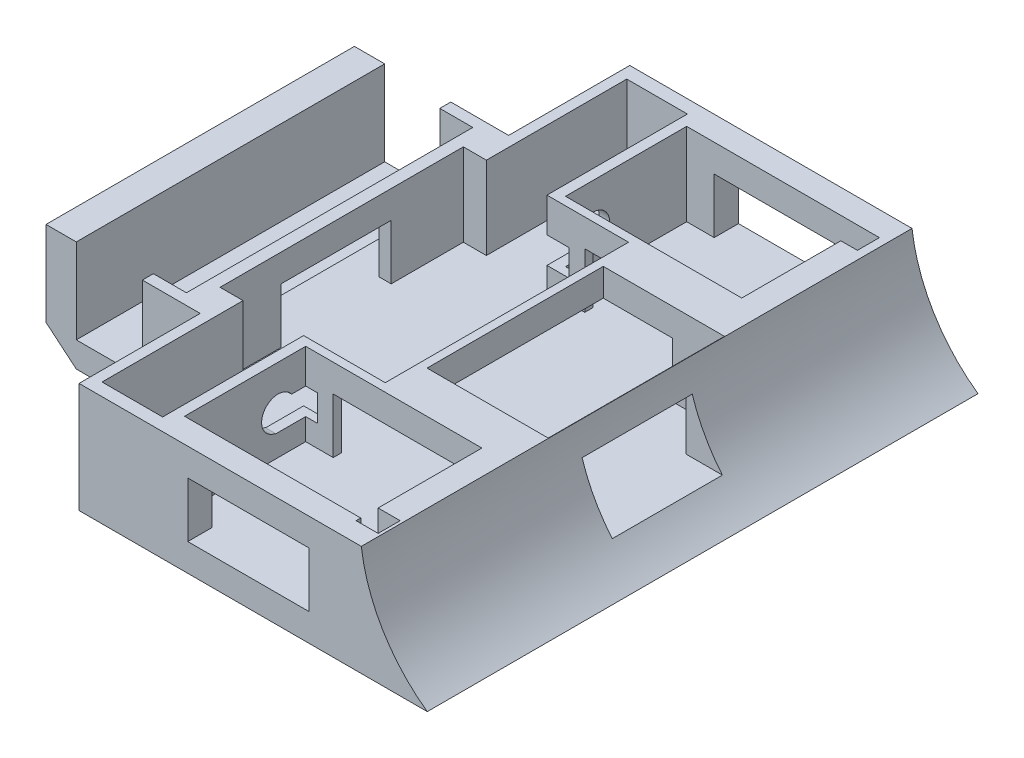
SolidWorks part; units mm, degrees
ref_plane "Front Plane" through (0, 0, 0) normal (0, 0, 1) x (1, 0, 0)
ref_plane "Top Plane" through (0, 0, 0) normal (0, 1, 0) x (1, 0, 0)
ref_plane "Right Plane" through (0, 0, 0) normal (1, 0, 0) x (0, 0, -1)
sketch "Sketch1" plane through (0, 0, 0) normal (0, 1, 0) x (1, 0, 0)
  line L1 (-50, -50) -> (50, -50)
  line L2 (-50, -50) -> (-50, 50)
  line L3 (-50, 50) -> (50, 50)
  line L4 (50, -50) -> (50, 50)
  line L5 (-50, -50) -> (50, 50) construction
  line L6 (-50, 50) -> (50, -50) construction
  point P0 (0, 0)
  dimension "D1" = 100
  dimension "D2" = 100
extrude "Boss-Extrude2" add sketch "Sketch1" along normal blind 40
sketch "Sketch3" plane through (50, 0, 0) normal (1, 0, 0) x (0, 0, -1)
  line L0 (-50, 40) -> (50, 40) construction
  line L1 (-11.0102, 5) -> (8.9898, 5)
  line L2 (-11.0102, 5) -> (-11.0102, 15)
  line L3 (-11.0102, 15) -> (8.9898, 15)
  line L4 (8.9898, 5) -> (8.9898, 15)
  line L5 (-11.0102, 5) -> (8.9898, 15) construction
  line L6 (-11.0102, 15) -> (8.9898, 5) construction
  line L8 (-50, 40) -> (-50, 0) construction
  point P0 (-1.0102, 10)
  point P7 (-50, 20)
  dimension "D1" = 20
  dimension "D2" = 10
  dimension "D3" = 30
  dimension "D4" = 50
extrude "Cut-Extrude3" cut sketch "Sketch3" against normal blind 100
sketch "Sketch4" plane through (0, 0, 50) normal (0, 0, 1) x (1, 0, 0)
  circle A0 centre (63.1914, 23.7473) radius 29.1799
extrude "Cut-Extrude5" cut sketch "Sketch4" against normal blind 100
sketch "Sketch5" plane through (0, 0, 50) normal (0, 0, 1) x (1, 0, 0)
  line L1 (-21.0432, 20) -> (38.9568, 20)
  line L2 (-21.0432, 20) -> (-21.0432, 40)
  line L3 (-21.0432, 40) -> (38.9568, 40)
  line L4 (38.9568, 20) -> (38.9568, 40)
  line L5 (-21.0432, 20) -> (38.9568, 40) construction
  line L6 (-21.0432, 40) -> (38.9568, 20) construction
  point P0 (8.9568, 30)
  dimension "D1" = 20
  dimension "D2" = 60
extrude "Cut-Extrude6" cut sketch "Sketch5" against normal blind 100
sketch "Sketch6" plane through (0, 20, 0) normal (0, 1, 0) x (1, 0, 0)
  line L1 (12.1904, -16) -> (34.1904, -16)
  line L2 (12.1904, -16) -> (12.1904, 16)
  line L3 (12.1904, 16) -> (34.1904, 16)
  line L4 (34.1904, -16) -> (34.1904, 16)
  line L5 (12.1904, -16) -> (34.1904, 16) construction
  line L6 (12.1904, 16) -> (34.1904, -16) construction
  point P0 (23.1904, 0)
  dimension "D1" = 32
  dimension "D2" = 22
extrude "Cut-Extrude7" cut sketch "Sketch6" against normal blind 15
sketch "Sketch7" plane through (0, 0, 50) normal (0, 0, 1) x (1, 0, 0)
  line L0 (-50, 0) -> (46.2347, 0) construction
  line L1 (2.7431, 15) -> (24.7431, 15)
  line L2 (2.7431, 15) -> (2.7431, 5)
  line L3 (2.7431, 5) -> (24.7431, 5)
  line L4 (24.7431, 15) -> (24.7431, 5)
  line L5 (2.7431, 15) -> (24.7431, 5) construction
  line L6 (2.7431, 5) -> (24.7431, 15) construction
  point P0 (13.7431, 10)
  dimension "D1" = 10
  dimension "D2" = 22
  dimension "D3" = 5
extrude "Cut-Extrude9" cut sketch "Sketch7" against normal blind 100
sketch "Sketch9" plane through (0, 20, 0) normal (0, 1, 0) x (1, 0, 0)
  line L1 (-2.2569, -45.5889) -> (29.7431, -45.5889)
  line L2 (-2.2569, -45.5889) -> (-2.2569, -23.5889)
  line L3 (-2.2569, -23.5889) -> (29.7431, -23.5889)
  line L4 (29.7431, -45.5889) -> (29.7431, -23.5889)
  line L5 (-2.2569, -45.5889) -> (29.7431, -23.5889) construction
  line L6 (-2.2569, -23.5889) -> (29.7431, -45.5889) construction
  point P0 (13.7431, -34.5889)
  dimension "D1" = 32
  dimension "D2" = 22
  dimension "D3" = 5
  dimension "D4" = 5
extrude "Cut-Extrude10" cut sketch "Sketch9" against normal blind 15
sketch "Sketch10" plane through (0, 20, 0) normal (0, 1, 0) x (1, 0, 0)
  line L0 (-2.2569, -45.5889) -> (29.7431, -45.5889) construction
  line L1 (29.7431, 45.59) -> (-2.2569, 45.59)
  line L2 (29.7431, 45.59) -> (29.7431, 23.59)
  line L3 (29.7431, 23.59) -> (-2.2569, 23.59)
  line L4 (-2.2569, 45.59) -> (-2.2569, 23.59)
  line L5 (29.7431, 45.59) -> (-2.2569, 23.59) construction
  line L6 (29.7431, 23.59) -> (-2.2569, 45.59) construction
  line L8 (-21.0432, 50) -> (34.2532, 50) construction
  point P0 (13.7431, 34.59)
  dimension "D1" = 32
  dimension "D2" = 22
  dimension "D3" = 4.41
  dimension "D4" = 5
extrude "Cut-Extrude11" cut sketch "Sketch10" against normal blind 15
sketch "Sketch11" plane through (0, 0, 50) normal (0, 0, 1) x (1, 0, 0)
  line L1 (-50, 0) -> (-17, 0)
  line L2 (-50, 0) -> (-50, 33)
  line L3 (-50, 33) -> (-17, 33)
  line L4 (-17, 0) -> (-17, 33)
  dimension "D1" = 33
  dimension "D2" = 33
extrude "Cut-Extrude13" cut sketch "Sketch11" against normal blind 22
sketch "Sketch12" plane through (0, 0, -50) normal (0, 0, -1) x (-1, 0, 0)
  line L1 (50, 0) -> (17, 0)
  line L2 (50, 0) -> (50, 33)
  line L3 (50, 33) -> (17, 33)
  line L4 (17, 0) -> (17, 33)
  dimension "D1" = 33
  dimension "D2" = 33
extrude "Cut-Extrude14" cut sketch "Sketch12" against normal blind 22
sketch "Sketch13" plane through (0, 0, -50) normal (0, 0, -1) x (-1, 0, 0)
  line L1 (21.0432, 40) -> (51.0432, 40)
  line L2 (21.0432, 40) -> (21.0432, 20)
  line L3 (21.0432, 20) -> (51.0432, 20)
  line L4 (51.0432, 40) -> (51.0432, 20)
  dimension "D1" = 30
  dimension "D2" = 20
extrude "Cut-Extrude15" cut sketch "Sketch13" against normal blind 100
sketch "Sketch14" plane through (0, 0, 28) normal (0, 0, 1) x (1, 0, 0)
  line L0 (-50, 20) -> (-50, 0) construction
  line L1 (-39.5, 4.5951) -> (-27.5, 4.5951)
  line L2 (-39.5, 4.5951) -> (-39.5, 20.5951)
  line L3 (-39.5, 20.5951) -> (-27.5, 20.5951)
  line L4 (-27.5, 4.5951) -> (-27.5, 20.5951)
  line L5 (-39.5, 4.5951) -> (-27.5, 20.5951) construction
  line L6 (-39.5, 20.5951) -> (-27.5, 4.5951) construction
  point P0 (-33.5, 12.5951)
  dimension "D1" = 12
  dimension "D2" = 16
  dimension "D3" = 10.5
extrude "Cut-Extrude17" cut sketch "Sketch14" against normal blind 80
sketch "Sketch15" plane through (0, 20, 0) normal (0, 1, 0) x (1, 0, 0)
  line L0 (-39.5, -28) -> (-39.5, 28) construction
  line L1 (-45.5, -26) -> (-21.5, -26)
  line L2 (-45.5, -26) -> (-45.5, 26)
  line L3 (-45.5, 26) -> (-21.5, 26)
  line L4 (-21.5, -26) -> (-21.5, 26)
  line L5 (-50, 28) -> (-39.5, 28) construction
  point P7 (-44.75, 28)
  dimension "D1" = 24
  dimension "D2" = 52
  dimension "D3" = 6
  dimension "D4" = 6
  dimension "D5" = 2
extrude "Cut-Extrude18" cut sketch "Sketch15" against normal blind 15
sketch "Sketch16" plane through (0, 20, 0) normal (0, 1, 0) x (1, 0, 0)
  line L0 (29.7431, -23.5889) -> (-2.2569, -23.5889) construction
  line L1 (-19.3096, 22.0911) -> (10.6904, 22.0911)
  line L2 (-19.3096, 22.0911) -> (-19.3096, -22.0889)
  line L3 (-19.3096, -22.0889) -> (10.6904, -22.0889)
  line L4 (10.6904, 22.0911) -> (10.6904, -22.0889)
  line L5 (-19.3096, 22.0911) -> (10.6904, -22.0889) construction
  line L6 (-19.3096, -22.0889) -> (10.6904, 22.0911) construction
  point P0 (-4.3096, 0.0011)
  dimension "D1" = 44.18
  dimension "D2" = 30
  dimension "D3" = 1.5
  dimension "D4" = 1.5
  dimension "D5" = 1.4989
extrude "Cut-Extrude19" cut sketch "Sketch16" against normal blind 15
sketch "Sketch17" plane through (0, 20, 0) normal (0, 1, 0) x (1, 0, 0)
  line L1 (-4.1269, 47.59) -> (-15.1269, 47.59)
  line L2 (-4.1269, 47.59) -> (-4.1269, 21.59)
  line L3 (-4.1269, 21.59) -> (-15.1269, 21.59)
  line L4 (-15.1269, 47.59) -> (-15.1269, 21.59)
  line L5 (-4.1269, 47.59) -> (-15.1269, 21.59) construction
  line L6 (-4.1269, 21.59) -> (-15.1269, 47.59) construction
  point P0 (-9.6269, 34.59)
  dimension "D1" = 26
  dimension "D2" = 11
  dimension "D3" = 2
  dimension "D4" = 2
  dimension "D5" = 1.87
  dimension "D6" = 1.8731
extrude "Cut-Extrude20" cut sketch "Sketch17" against normal blind 15
sketch "Sketch18" plane through (0, 20, 0) normal (0, 1, 0) x (1, 0, 0)
  line L1 (-15.13, -21.6911) -> (-4.13, -21.6911)
  line L2 (-15.13, -21.6911) -> (-15.13, -47.6911)
  line L3 (-15.13, -47.6911) -> (-4.13, -47.6911)
  line L4 (-4.13, -21.6911) -> (-4.13, -47.6911)
  line L5 (-15.13, -21.6911) -> (-4.13, -47.6911) construction
  line L6 (-15.13, -47.6911) -> (-4.13, -21.6911) construction
  point P0 (-9.63, -34.6911)
  dimension "D1" = 26
  dimension "D2" = 11
  dimension "D3" = 1.87
  dimension "D4" = 1.8731
extrude "Cut-Extrude22" cut sketch "Sketch18" against normal blind 15
sketch "Sketch19" plane through (0, 0, 0) normal (0, -1, 0) x (-1, 0, 0)
  line L0 (-46.2347, -50) -> (-46.2347, 50) construction
  line L1 (-43.2347, -45) -> (-32.2347, -45)
  line L2 (-43.2347, -45) -> (-43.2347, -28)
  line L3 (-43.2347, -28) -> (-32.2347, -28)
  line L4 (-32.2347, -45) -> (-32.2347, -28)
  line L5 (-43.2347, -45) -> (-32.2347, -28) construction
  line L6 (-43.2347, -28) -> (-32.2347, -45) construction
  line L7 (17, -50) -> (-46.2347, -50) construction
  point P0 (-37.7347, -36.5)
  dimension "D1" = 17
  dimension "D2" = 11
  dimension "D3" = 3
  dimension "D4" = 5
extrude "Cut-Extrude26" cut sketch "Sketch19" against normal blind 2.2
sketch "Sketch20" plane through (0, 0, 0) normal (0, -1, 0) x (-1, 0, 0)
  circle A0 centre (-32.2347, -45) radius 2.5
extrude "Cut-Extrude32" cut sketch "Sketch20" against normal blind 17
sketch "Sketch21" plane through (29.7431, 0, 0) normal (-1, 0, 0) x (0, 0, 1)
  line L0 (45.5889, 20) -> (23.5889, 20) construction
  line L1 (46.4334, 20) -> (42.4334, 20)
  line L2 (46.4334, 20) -> (46.4334, 8)
  line L3 (46.4334, 8) -> (42.4334, 8)
  line L4 (42.4334, 20) -> (42.4334, 8)
  dimension "D1" = 4
  dimension "D2" = 12
extrude "Cut-Extrude33" cut sketch "Sketch21" against normal blind 4
sketch "Sketch23" plane through (0, 0, 0) normal (0, -1, 0) x (-1, 0, 0)
  line L0 (-46.2347, 50) -> (17, 50) construction
  line L1 (-32.2347, 45) -> (-43.2347, 45)
  line L2 (-32.2347, 45) -> (-32.2347, 28)
  line L3 (-32.2347, 28) -> (-43.2347, 28)
  line L4 (-43.2347, 45) -> (-43.2347, 28)
  line L5 (-46.2347, -50) -> (-46.2347, 50) construction
  dimension "D1" = 17
  dimension "D2" = 11
  dimension "D3" = 5
  dimension "D4" = 3
extrude "Cut-Extrude34" cut sketch "Sketch23" against normal blind 2.2
sketch "Sketch24" plane through (0, 0, 0) normal (0, -1, 0) x (1, 0, 0)
  circle A0 centre (32.2347, -45) radius 2.5
extrude "Cut-Extrude35" cut sketch "Sketch24" against normal blind 17
sketch "Sketch25" plane through (29.7431, 0, 0) normal (-1, 0, 0) x (0, 0, 1)
  line L1 (-45.59, 20) -> (-41.59, 20)
  line L2 (-45.59, 20) -> (-45.59, 8)
  line L3 (-45.59, 8) -> (-41.59, 8)
  line L4 (-41.59, 20) -> (-41.59, 8)
  dimension "D1" = 4
  dimension "D2" = 12
extrude "Cut-Extrude36" cut sketch "Sketch25" against normal blind 3
sketch "Sketch26" plane through (-2.2569, 0, 0) normal (1, 0, 0) x (0, 0, -1)
  line L0 (-23.5889, 20) -> (-45.5889, 20) construction
  line L1 (-23.5889, 5) -> (-23.5889, 20) construction
  circle A0 centre (-28.5889, 12) radius 3
  dimension "D1" = 8
  dimension "D2" = 5
extrude "Cut-Extrude37" cut sketch "Sketch26" against normal blind 3
sketch "Sketch27" plane through (-2.2569, 0, 0) normal (1, 0, 0) x (0, 0, -1)
  line L0 (23.59, 5) -> (23.59, 20) construction
  line L1 (45.59, 20) -> (23.59, 20) construction
  circle A0 centre (28.59, 12) radius 3
  point P2 (23.59, 12.5)
  dimension "D1" = 5
  dimension "D2" = 8
extrude "Cut-Extrude38" cut sketch "Sketch27" against normal blind 3
sketch "Sketch28" plane through (0, 0, 0) normal (0, -1, 0) x (1, 0, 0)
  line L0 (-17, -28) -> (-50, -28) construction
  line L1 (-48.5559, -5.5) -> (-31.5559, -5.5)
  line L2 (-48.5559, -5.5) -> (-48.5559, 5.5)
  line L3 (-48.5559, 5.5) -> (-31.5559, 5.5)
  line L4 (-31.5559, -5.5) -> (-31.5559, 5.5)
  line L5 (-50, 28) -> (-17, 28) construction
  dimension "D1" = 11
  dimension "D2" = 17
  dimension "D3" = 22.5
  dimension "D4" = 22.5
extrude "Cut-Extrude39" cut sketch "Sketch28" against normal blind 2.2
sketch "Sketch29" plane through (0, 2.2, 0) normal (0, -1, 0) x (-1, 0, 0)
  circle A0 centre (47.7999, -0.0702) radius 3
extrude "Cut-Extrude40" cut sketch "Sketch29" against normal blind 4
sketch "Sketch30" plane through (0, 0, -22.0911) normal (0, 0, 1) x (1, 0, 0)
  line L0 (-4.1269, 20) -> (-4.1269, 5) construction
  line L1 (-4.1269, 8.9494) -> (-0.1269, 8.9494)
  line L2 (-4.1269, 8.9494) -> (-4.1269, 13.7494)
  line L3 (-4.1269, 13.7494) -> (-0.1269, 13.7494)
  line L4 (-0.1269, 8.9494) -> (-0.1269, 13.7494)
  dimension "D1" = 4.8
  dimension "D2" = 4
extrude "Cut-Extrude43" cut sketch "Sketch30" against normal blind 7
sketch "Sketch31" plane through (0, 0, 22.0889) normal (0, 0, -1) x (-1, 0, 0)
  line L0 (4.13, 5) -> (4.13, 20) construction
  line L1 (4.13, 8.95) -> (0.13, 8.95)
  line L2 (4.13, 8.95) -> (4.13, 13.75)
  line L3 (4.13, 13.75) -> (0.13, 13.75)
  line L4 (0.13, 8.95) -> (0.13, 13.75)
  dimension "D1" = 4
  dimension "D2" = 4.8
  dimension "D3" = 6.25
extrude "Cut-Extrude44" cut sketch "Sketch31" against normal blind 7
sketch "Sketch33" plane through (0, 0, -28) normal (0, 0, -1) x (-1, 0, 0)
  line L0 (45, 0) -> (50, 5)
  line L1 (50, 0) -> (45, 0)
  line L2 (50, 0) -> (50, 5)
  dimension "D2" = 5
extrude "Cut-Extrude45" cut sketch "Sketch33" against normal blind 100
sketch "Sketch34" plane through (0, 0, 28) normal (0, 0, 1) x (1, 0, 0)
  line L1 (-50, 20) -> (-45, 20)
  line L2 (-50, 20) -> (-50, 0)
  line L3 (-50, 0) -> (-45, 0)
  line L4 (-45, 20) -> (-45, 0)
extrude "Cut-Extrude46" cut sketch "Sketch34" against normal blind 100
sketch "Sketch35" plane through (0, 0, 28) normal (0, 0, 1) x (1, 0, 0)
  line L0 (-45, 4.5951) -> (-39.5, 0)
  line L1 (-45, 0) -> (-39.5, 0)
  line L2 (-45, 0) -> (-45, 4.5951)
extrude "Cut-Extrude47" cut sketch "Sketch35" against normal blind 100
sketch "Sketch36" plane through (0, 0, 28) normal (0, 0, 1) x (1, 0, 0)
  line L1 (-45, 20) -> (-39.5, 20)
  line L2 (-45, 20) -> (-45, 4.5951)
  line L3 (-45, 4.5951) -> (-39.5, 4.5951)
  line L4 (-39.5, 20) -> (-39.5, 4.5951)
extrude "Boss-Extrude3" add sketch "Sketch36" against normal blind 55
sketch "Sketch37" plane through (0, 0, 0) normal (0, -1, 0) x (-1, 0, 0)
  line L1 (42.1332, -5.5) -> (21.901, -5.5)
  line L2 (42.1332, -5.5) -> (42.1332, 5.5)
  line L3 (42.1332, 5.5) -> (21.901, 5.5)
  line L4 (21.901, -5.5) -> (21.901, 5.5)
extrude "Cut-Extrude48" cut sketch "Sketch37" against normal blind 3
sketch "Sketch38" plane through (0, 3, 0) normal (0, -1, 0) x (-1, 0, 0)
  line L0 (17, -50) -> (-46.2347, -50) construction
  line L1 (13.2221, -43) -> (-26.7779, -43)
  line L2 (13.2221, -43) -> (13.2221, 43)
  line L3 (13.2221, 43) -> (-26.7779, 43)
  line L4 (-26.7779, -43) -> (-26.7779, 43)
  dimension "D1" = 86
  dimension "D2" = 40
  dimension "D3" = 7
extrude "Cut-Extrude53" cut sketch "Sketch38" against normal blind 1
